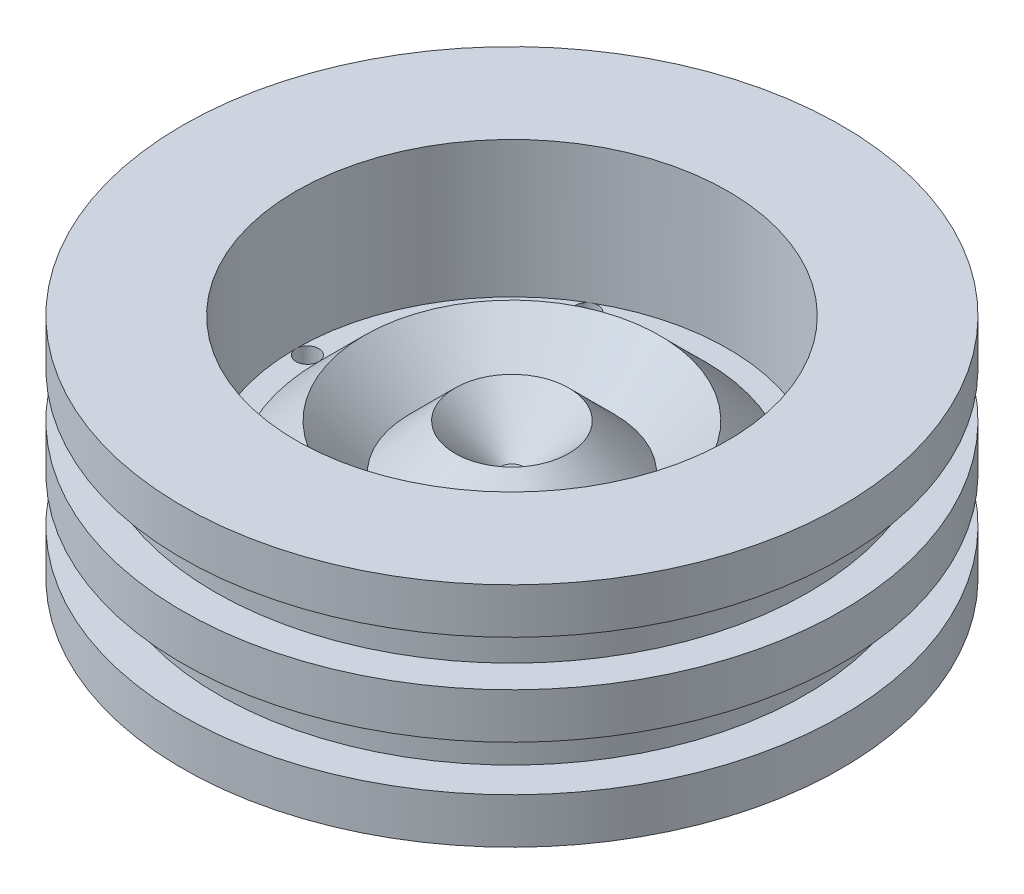
SolidWorks part; units mm, degrees
ref_plane "Front Plane" through (0, 0, 0) normal (0, 0, 1) x (1, 0, 0)
ref_plane "Top Plane" through (0, 0, 0) normal (0, 1, 0) x (1, 0, 0)
ref_plane "Right Plane" through (0, 0, 0) normal (1, 0, 0) x (0, 0, -1)
sketch "Sketch1" plane through (0, 0, 0) normal (0, 0, 1) x (1, 0, 0)
  line L0 (0, 0) -> (-72.5, 0)
  line L1 (-72.5, 0) -> (-72.5, 10)
  line L2 (-72.5, 10) -> (-64.5, 10)
  line L3 (-64.5, 10) -> (-64.5, 20)
  line L4 (-64.5, 20) -> (-72.5, 20)
  line L5 (-72.5, 20) -> (-72.5, 30)
  line L6 (-72.5, 30) -> (-65.3263, 30)
  line L7 (-65.3263, 30) -> (-65.3263, 40)
  line L8 (-65.3263, 40) -> (-72.5, 40)
  line L9 (-72.5, 40) -> (-72.5, 50)
  line L10 (-72.5, 50) -> (-47.5, 50)
  line L12 (-47.5, 50) -> (-72.5, 50)
  line L13 (-47.5, 50) -> (-47.5, 20)
  line L14 (-12.5, 30) -> (-2.5, 20)
  line L15 (-2.5, 20) -> (0, 20)
  line L18 (0, 20) -> (0, 0)
  line L23 (-47.5, 20) -> (-42.5, 20)
  line L44 (-12.5, 30) -> (-22.5, 20)
  line L45 (-22.5, 20) -> (-32.5, 30)
  line L46 (-32.5, 30) -> (-42.5, 20)
  dimension "D1" = 72.5
  dimension "D2" = 5
  dimension "D3" = 8
  dimension "D4" = 10
  dimension "D5" = 10
  dimension "D6" = 10
  dimension "D7" = 10
  dimension "D8" = 25
  dimension "D9" = 10
  dimension "D10" = 20
  dimension "D11" = 45
  dimension "D12" = 0
  dimension "D13" = 20
  dimension "D14" = 20
  dimension "D15" = 90
  dimension "D16" = 20
  dimension "D17" = 30
revolve "Revolve1" add sketch "Sketch1" angle 360 about L18
sketch "Sketch2" plane through (0, 0, 0) normal (0, -1, 0) x (1, 0, 0)
  line L0 (0, 0) -> (-42.5, 0)
  line L1 (0, 0) -> (-72.5, 0) construction
  line L2 (-42.5, 0) -> (-47.5, 0)
  circle A0 centre (-45, 0) radius 2.5
  circle A1 centre (-22.5, 38.9711) radius 2.5
  circle A2 centre (22.5, 38.9711) radius 2.5
  circle A3 centre (45, 0) radius 2.5
  circle A4 centre (22.5, -38.9711) radius 2.5
  circle A5 centre (-22.5, -38.9711) radius 2.5
  point P20 (0, 0)
  dimension "D1" = 42.5
  dimension "D2" = 5
  dimension "D3" = 6
extrude "Cut-Extrude1" cut sketch "Sketch2" against normal blind 30 contours L2 A0 | L2 A0 | A5 | A1 | A2 | A3 | A4
